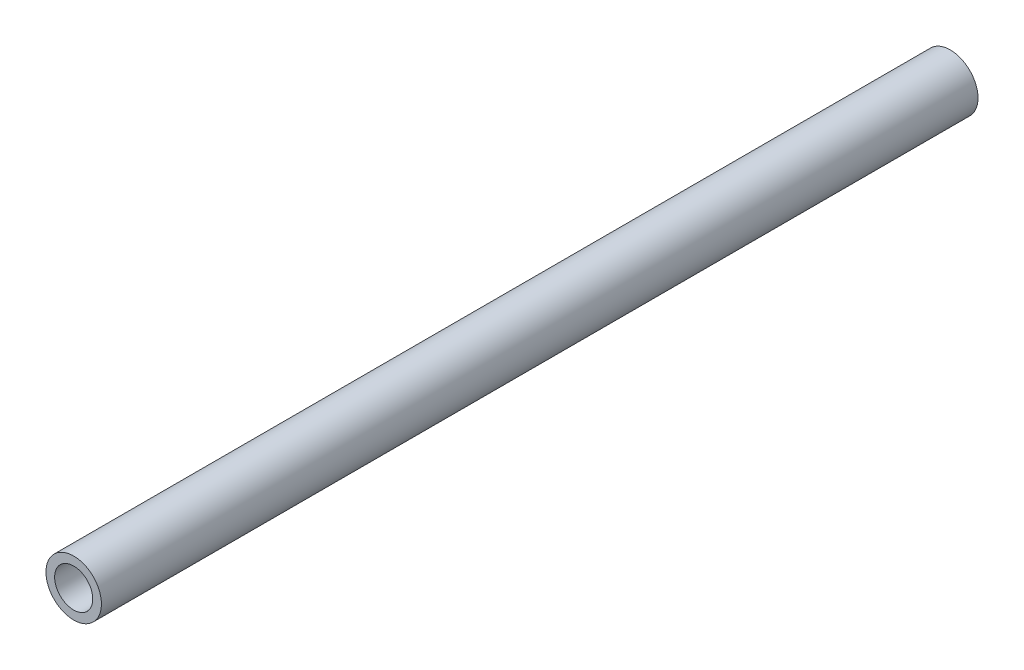
SolidWorks part; units mm, degrees
material "Cast Carbon Steel"
ref_plane "Front Plane" through (0, 0, 0) normal (0, 0, 1) x (1, 0, 0)
ref_plane "Top Plane" through (0, 0, 0) normal (0, 1, 0) x (1, 0, 0)
ref_plane "Right Plane" through (0, 0, 0) normal (1, 0, 0) x (0, 0, -1)
sketch "Sketch1" plane through (0, 0, 0) normal (0, 0, 1) x (1, 0, 0)
  circle A0 centre (0, 0) radius 12.7
  circle A1 centre (0, 0) radius 8.7312
  dimension "D1" = 25.4
  dimension "D2" = 17.4625
extrude "Boss-Extrude1" add sketch "Sketch1" against normal blind 401.32
